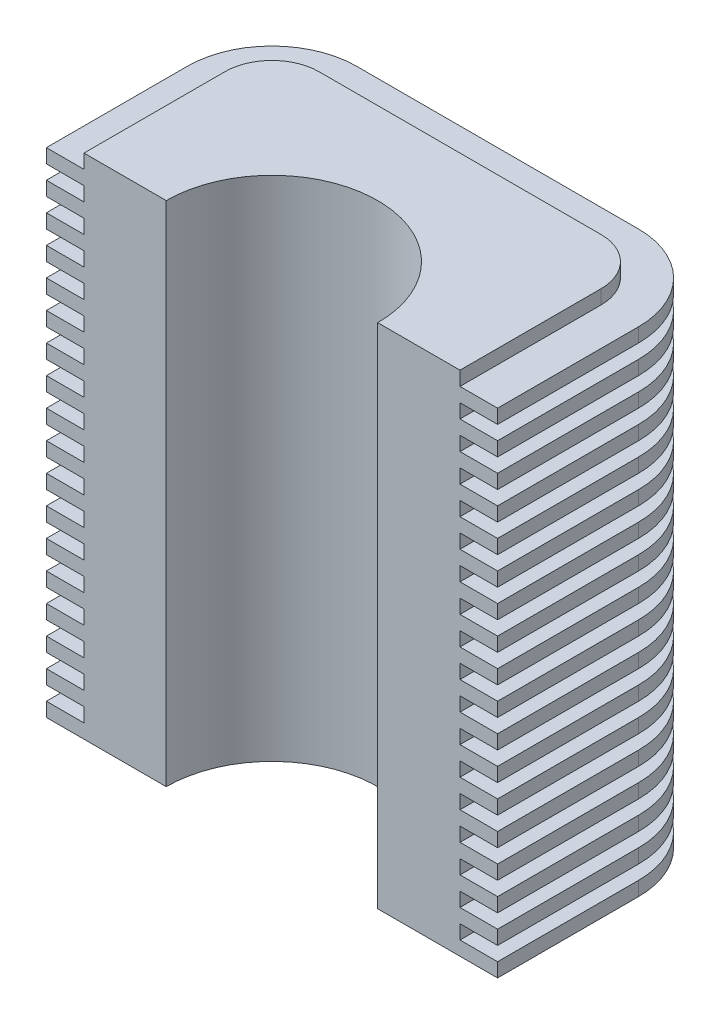
SolidWorks part; units mm, degrees
ref_plane "Front Plane" through (0, 0, 0) normal (0, 0, 1) x (1, 0, 0)
ref_plane "Top Plane" through (0, 0, 0) normal (0, 1, 0) x (1, 0, 0)
ref_plane "Right Plane" through (0, 0, 0) normal (1, 0, 0) x (0, 0, -1)
sketch "Szkic1" plane through (0, 0, 0) normal (0, 1, 0) x (1, 0, 0)
  line L0 (0, 0) -> (0, 40)
  line L1 (0, 40) -> (80, 40)
  line L2 (80, 40) -> (80, 0)
  line L3 (80, 0) -> (62.5, 0)
  line L4 (17.5, 0) -> (0, 0)
  arc A0 (62.5, 0) -> (17.5, 0) centre (40, 0) ccw
  dimension "D3" = 22.5
  dimension "D1" = 40
  dimension "D2" = 80
extrude "Dodanie-wyciągnięcie1" add sketch "Szkic1" along normal blind 108
fillet "Zaokrąglenie1" radius 10 2 edges at (80, 54, -40) (0, 54, -40)
sketch "Szkic2" plane through (0, 0, 0) normal (0, -1, 0) x (1, 0, 0)
  line L0 (80, 0) -> (80, -30) construction
  line L1 (70, -40) -> (10, -40) construction
  line L2 (0, -30) -> (0, 0) construction
  line L3 (80, 0) -> (80, -30)
  line L4 (70, -40) -> (10, -40)
  line L5 (0, -30) -> (0, 0)
  line L6 (88, 0) -> (88, -30)
  line L7 (70, -48) -> (10, -48)
  line L8 (-8, -30) -> (-8, 0)
  line L9 (-8, 0) -> (0, 0)
  line L10 (80, 0) -> (88, 0)
  arc A0 (70, -40) -> (80, -30) centre (70, -30) ccw construction
  arc A1 (0, -30) -> (10, -40) centre (10, -30) ccw construction
  arc A2 (70, -40) -> (80, -30) centre (70, -30) ccw
  arc A3 (0, -30) -> (10, -40) centre (10, -30) ccw
  arc A4 (70, -48) -> (88, -30) centre (70, -30) ccw
  arc A5 (-8, -30) -> (10, -48) centre (10, -30) ccw
  dimension "D1" = 8
extrude "Dodanie-wyciągnięcie2" add sketch "Szkic2" against normal blind 3
pattern_linear "Szyk liniowy1" count 18 spacing 6 along (0, 1, 0) of "Dodanie-wyciągnięcie2"
